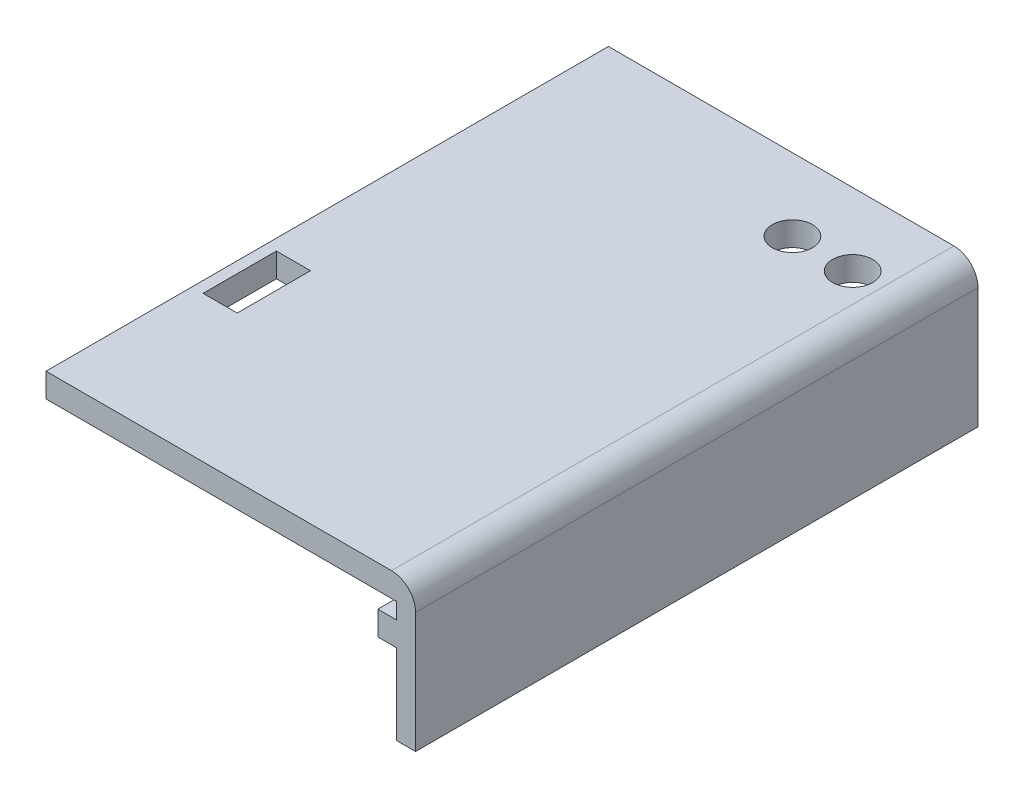
SolidWorks part; units mm, degrees
ref_plane "Front Plane" through (0, 0, 0) normal (0, 0, 1) x (1, 0, 0)
ref_plane "Top Plane" through (0, 0, 0) normal (0, 1, 0) x (1, 0, 0)
ref_plane "Right Plane" through (0, 0, 0) normal (1, 0, 0) x (0, 0, -1)
sketch "Sketch1" plane through (0, 0, 0) normal (0, 0, 1) x (1, 0, 0)
  line L1 (-23, 9) -> (23, 9) construction
  line L2 (-23, 9) -> (-23, -9) construction
  line L3 (-23, -9) -> (23, -9) construction
  line L4 (23, 9) -> (23, -9) construction
  line L5 (-23, 9) -> (23, 9)
  line L6 (-23, 9) -> (-23, 6)
  line L7 (-23, 6) -> (20.6, 6)
  line L9 (23, -9) -> (20.6, -9)
  line L10 (23, -9) -> (23, 9)
  line L12 (20.6, -9) -> (20.6, 6)
  point P4 (0, 9)
  point P6 (23, 0)
  dimension "D1" = 46
  dimension "D2" = 18
  dimension "D3" = 3
  dimension "D4" = 2.4
extrude "Extrude1" add sketch "Sketch1" along normal blind 70
sketch "Sketch2" plane through (20.6, 0, 0) normal (-1, 0, 0) x (0, 0, 1)
  line L0 (0, 6) -> (0, -9) construction
  line L1 (0, 1) -> (3, 1)
  line L2 (0, 1) -> (0, 4)
  line L3 (0, 4) -> (3, 4)
  line L4 (3, 1) -> (3, 4)
  line L5 (70, 6) -> (70, -9) construction
  line L6 (70, 1) -> (67, 1)
  line L7 (70, 1) -> (70, 4)
  line L8 (70, 4) -> (67, 4)
  line L9 (67, 1) -> (67, 4)
  line L11 (70, 6) -> (0, 6) construction
  dimension "D1" = 3
  dimension "D2" = 3
  dimension "D3" = 2
extrude "Extrude2" add sketch "Sketch2" along normal blind 2.3
sketch "Sketch3" plane through (0, 6, 0) normal (0, -1, 0) x (1, 0, 0)
  line L0 (-23, 70) -> (-23, 0) construction
  line L1 (-23, 5.5) -> (-19, 5.5)
  line L2 (-23, 5.5) -> (-23, 10.5)
  line L3 (-23, 10.5) -> (-19, 10.5)
  line L4 (-19, 5.5) -> (-19, 10.5)
  line L5 (-23, 0) -> (20.6, 0) construction
  line L6 (-23, 64.5) -> (-19, 64.5)
  line L7 (-23, 64.5) -> (-23, 59.5)
  line L8 (-23, 59.5) -> (-19, 59.5)
  line L9 (-19, 64.5) -> (-19, 59.5)
  line L10 (-23, 70) -> (20.6, 70) construction
  dimension "D1" = 5.5
  dimension "D2" = 5
  dimension "D3" = 4
  dimension "D4" = 5.5
extrude "Extrude3" add sketch "Sketch3" along normal blind 2
sketch "Sketch4" plane through (-23, 0, 0) normal (-1, 0, 0) x (0, 0, 1)
  line L0 (0, 9) -> (0, 6) construction
  line L1 (70, 9) -> (70, 6) construction
  line L2 (70, 9) -> (0, 9) construction
  circle A0 centre (8, 6.75) radius 1
  circle A1 centre (62, 6.75) radius 1
  dimension "D1" = 2
  dimension "D2" = 8
  dimension "D3" = 8
  dimension "D4" = 2.25
extrude "Extrude4" cut sketch "Sketch4" against normal blind 5
fillet "Fillet1" radius 3 1 edges at (23, 9, 35)
sketch "Sketch5" plane through (0, 9, 0) normal (0, 1, 0) x (-1, 0, 0)
  line L0 (-23, 0) -> (-23, 70) construction
  line L1 (-20, 0) -> (23, 0) construction
  circle A0 centre (-16.4, 9) radius 2.5
  circle A1 centre (-8.9, 9) radius 2.5
  dimension "D3" = 5
  dimension "D1" = 6.6
  dimension "D2" = 7.5
  dimension "D4" = 9
extrude "Extrude6" cut sketch "Sketch5" against normal blind 5
sketch "Sketch6" plane through (0, 9, 0) normal (0, 1, 0) x (-1, 0, 0)
  line L1 (21.6134, 42.7111) -> (17.366, 42.7111)
  line L2 (21.6134, 42.7111) -> (21.6134, 51.8361)
  line L3 (21.6134, 51.8361) -> (17.366, 51.8361)
  line L4 (17.366, 42.7111) -> (17.366, 51.8361)
extrude "Cut-Extrude1" cut sketch "Sketch6" against normal blind 10
